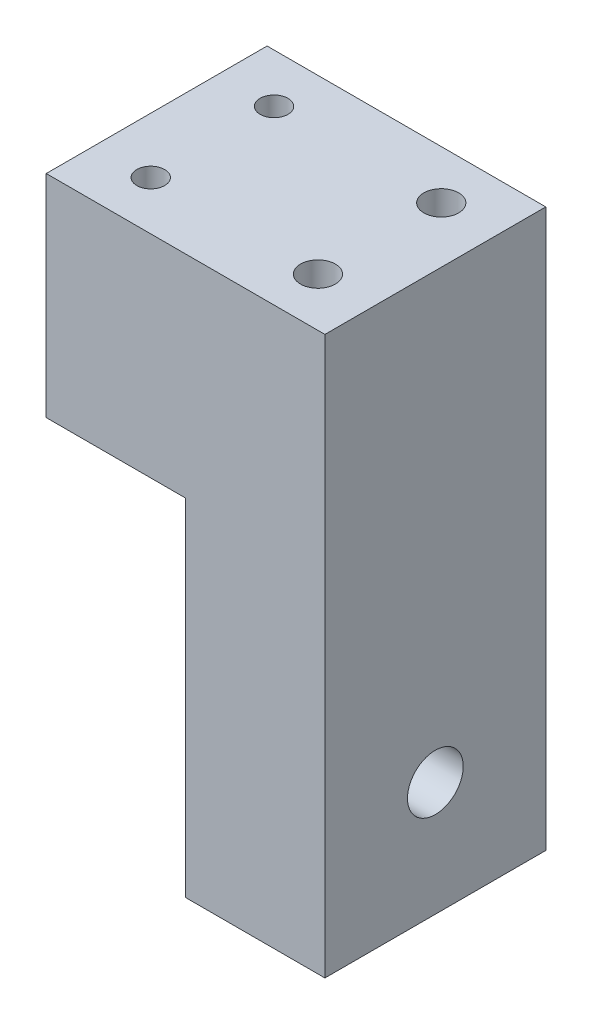
SolidWorks part; units mm, degrees
material "6061-T6 (SS)"
ref_plane "Front Plane" through (0, 0, 0) normal (0, 0, 1) x (1, 0, 0)
ref_plane "Top Plane" through (0, 0, 0) normal (0, 1, 0) x (1, 0, 0)
ref_plane "Right Plane" through (0, 0, 0) normal (1, 0, 0) x (0, 0, -1)
sketch "Sketch1" plane through (0, 0, 0) normal (0, 1, 0) x (1, 0, 0)
  line L1 (-4.3431, 11.7969) -> (15.6569, 11.7969)
  line L2 (-4.3431, 11.7969) -> (-4.3431, -19.9031)
  line L3 (-4.3431, -19.9031) -> (15.6569, -19.9031)
  line L4 (15.6569, 11.7969) -> (15.6569, -19.9031)
  line L5 (-4.3431, 11.7969) -> (15.6569, -19.9031) construction
  line L6 (-4.3431, -19.9031) -> (15.6569, 11.7969) construction
  point P4 (5.6569, -4.0531)
  dimension "D1" = 20
  dimension "D2" = 31.7
extrude "Boss-Extrude1" add sketch "Sketch1" along normal blind 80
sketch "Sketch2" plane through (-4.3431, 0, 0) normal (-1, 0, 0) x (0, 0, 1)
  circle A0 centre (4.0531, 16.3904) radius 4
  dimension "D1" = 8
extrude "Cut-Extrude1" cut sketch "Sketch2" against normal up to next
hole_wizard "M3x0.5 Tapped Hole1" positions "Sketch3" profile "Sketch4" tap size "M3x0.5" standard "ANSI Metric"
sketch "Sketch3" plane through (-4.3431, 0, 0) normal (-1, 0, 0) x (0, 0, 1)
  point P0 (16.6043, 28.9415)
  point P3 (-8.498, 28.9415)
  point P6 (-8.498, 3.8392)
  point P9 (16.6043, 3.8392)
sketch "Sketch4" plane through (-4.3431, 28.9415, 16.6043) normal (0, 1, 0) x (0, 0, 1)
  line L0 (0, 0) -> (0, 8.2511)
  line L1 (0, 8.2511) -> (1.25, 7.5)
  line L2 (1.25, 7.5) -> (1.25, 0)
  line L5 (1.25, 0) -> (0, 0)
  line L10 (0, 8.2511) -> (-1.25, 7.5) construction
  line L11 (0, -6.35) -> (0, 107.95) construction
  dimension "Tap Drill Dia." = 2.5
  dimension "Tap Drill Depth" = 7.5
  dimension "Drill Angle" = 118
cosmetic thread "Hole Thread1" parameters "D1"=6, "D2"=3
cosmetic thread "Hole Thread2" parameters "D1"=6, "D2"=3
cosmetic thread "Hole Thread3" parameters "D1"=6, "D2"=3
cosmetic thread "Hole Thread4" parameters "D1"=6, "D2"=3
sketch "Sketch5" plane through (-4.3431, 0, 0) normal (-1, 0, 0) x (0, 0, 1)
  line L0 (-11.7969, 80) -> (-11.7969, 0) construction
  line L1 (-11.7969, 49.6555) -> (19.9031, 49.6555)
  line L2 (-11.7969, 49.6555) -> (-11.7969, 80)
  line L3 (-11.7969, 80) -> (19.9031, 80)
  line L4 (19.9031, 49.6555) -> (19.9031, 80)
  line L5 (-11.7969, 49.6555) -> (19.9031, 80) construction
  line L6 (-11.7969, 80) -> (19.9031, 49.6555) construction
  point P4 (4.0531, 64.8277)
extrude "Boss-Extrude2" add sketch "Sketch5" along normal blind 20
hole_wizard "Ø4.0mm Dowel Hole1" positions "Sketch8" profile "Sketch7" hole size "Ø4.0" standard "ANSI Metric"
sketch "Sketch8" plane through (0, 80, 0) normal (0, 1, 0) x (1, 0, 0)
  line L0 (15.6569, 11.7969) -> (-24.3431, 11.7969) construction
  line L1 (-24.3431, -19.9031) -> (15.6569, -19.9031) construction
  line L2 (-24.3431, -19.9031) -> (-24.3431, 11.7969) construction
  point P0 (-16.3431, 4.7969)
  point P2 (-16.3431, -12.9031)
  dimension "D1" = 7
  dimension "D2" = 7
  dimension "D3" = 8
sketch "Sketch7" plane through (-16.3431, 80, -4.7969) normal (1, 0, 0) x (0, 0, 1)
  line L0 (0, 0) -> (0, 6.4017)
  line L1 (0, 6.4017) -> (2, 5.2)
  line L2 (2, 5.2) -> (2, 0)
  line L5 (2, 0) -> (0, 0)
  line L10 (0, 6.4017) -> (-2, 5.2) construction
  line L11 (0, -6.35) -> (0, 107.95) construction
  dimension "Hole Dia." = 4
  dimension "Hole Depth" = 5.2
  dimension "Drill Angle" = 118
hole_wizard "M6x1.0 Tapped Hole1" positions "Sketch9" profile "Sketch10" tap size "M6x1.0" standard "ANSI Metric"
sketch "Sketch9" plane through (0, 80, 0) normal (0, 1, 0) x (1, 0, 0)
  line L0 (15.6569, -19.9031) -> (15.6569, 11.7969) construction
  line L1 (15.6569, 11.7969) -> (-24.3431, 11.7969) construction
  line L2 (-24.3431, -19.9031) -> (15.6569, -19.9031) construction
  point P0 (7.6569, 4.7969)
  point P2 (7.6569, -12.9031)
  dimension "D1" = 8
  dimension "D2" = 7
  dimension "D3" = 7
sketch "Sketch10" plane through (7.6569, 80, -4.7969) normal (1, 0, 0) x (0, 0, 1)
  line L0 (0, 0) -> (0, 16.5022)
  line L1 (0, 16.5022) -> (2.5, 15)
  line L2 (2.5, 15) -> (2.5, 0)
  line L5 (2.5, 0) -> (0, 0)
  line L10 (0, 16.5022) -> (-2.5, 15) construction
  line L11 (0, -6.35) -> (0, 107.95) construction
  dimension "Tap Drill Dia." = 5
  dimension "Tap Drill Depth" = 15
  dimension "Drill Angle" = 118
cosmetic thread "Hole Thread5" parameters "D1"=12, "D2"=6
cosmetic thread "Hole Thread6" parameters "D1"=12, "D2"=6
